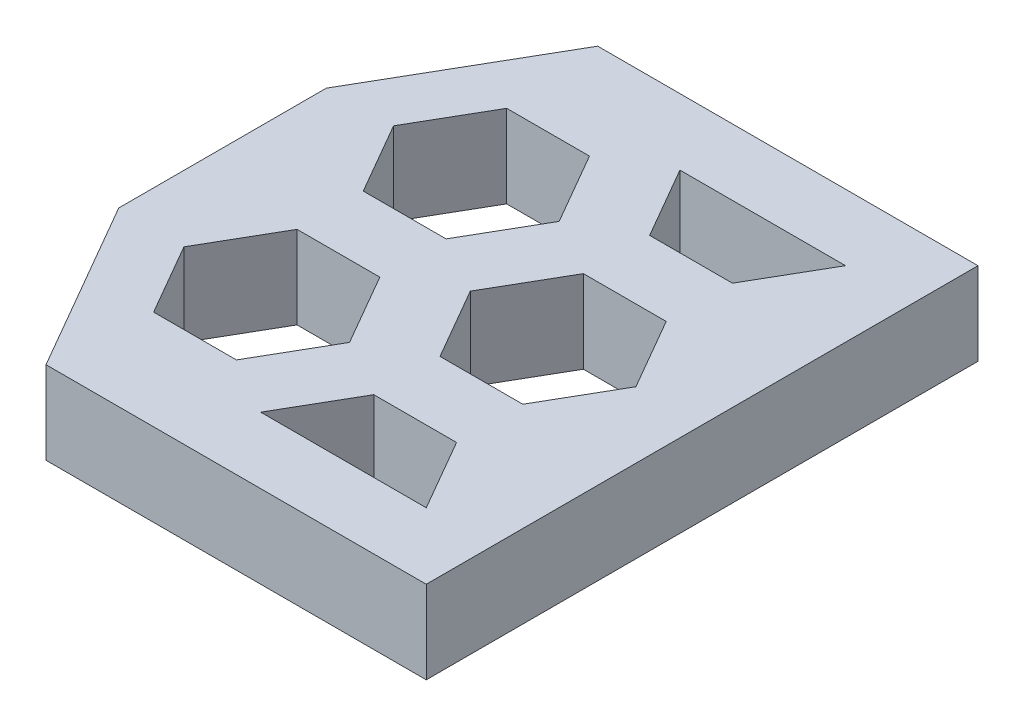
SolidWorks part; units mm, degrees
ref_plane "Front Plane" through (0, 0, 0) normal (0, 0, 1) x (1, 0, 0)
ref_plane "Top Plane" through (0, 0, 0) normal (0, 1, 0) x (1, 0, 0)
ref_plane "Right Plane" through (0, 0, 0) normal (1, 0, 0) x (0, 0, -1)
sketch "Sketch1" plane through (0, 0, 0) normal (0, 1, 0) x (1, 0, 0)
  line L0 (7.4821, 14.6603) -> (12.4821, 14.6603)
  line L1 (0, 0) -> (14.4821, 0)
  line L2 (0, 0) -> (0, 16.6603)
  line L3 (0, 16.6603) -> (14.4821, 16.6603)
  line L4 (14.4821, 0) -> (14.4821, 16.6603)
  line L5 (7, 11.4952) -> (5.75, 13.6603)
  line L6 (5.75, 13.6603) -> (3.25, 13.6603)
  line L7 (3.25, 13.6603) -> (2, 11.4952)
  line L8 (2, 11.4952) -> (3.25, 9.3301)
  line L9 (3.25, 9.3301) -> (5.75, 9.3301)
  line L10 (5.75, 9.3301) -> (7, 11.4952)
  line L11 (7, 5.1651) -> (5.75, 7.3301)
  line L12 (5.75, 7.3301) -> (3.25, 7.3301)
  line L13 (3.25, 7.3301) -> (2, 5.1651)
  line L14 (2, 5.1651) -> (3.25, 3)
  line L15 (3.25, 3) -> (5.75, 3)
  line L16 (5.75, 3) -> (7, 5.1651)
  line L17 (12.4821, 8.3301) -> (11.2321, 10.4952)
  line L18 (11.2321, 10.4952) -> (8.7321, 10.4952)
  line L19 (8.7321, 10.4952) -> (7.4821, 8.3301)
  line L20 (7.4821, 8.3301) -> (8.7321, 6.1651)
  line L21 (8.7321, 6.1651) -> (11.2321, 6.1651)
  line L22 (11.2321, 6.1651) -> (12.4821, 8.3301)
  line L26 (7.4821, 14.6603) -> (8.7321, 12.4952)
  line L27 (8.7321, 12.4952) -> (11.2321, 12.4952)
  line L28 (11.2321, 12.4952) -> (12.4821, 14.6603)
  line L29 (11.2321, 16.8253) -> (9.9821, 16.8253) [skipped]
  line L30 (11.9047, 15.6603) -> (11.8571, 15.7428) [skipped]
  line L31 (7.674, 14.9928) -> (7.6264, 14.9103) [skipped]
  line L32 (7.4821, 2) -> (12.4821, 2)
  line L33 (12.4821, 2) -> (11.2321, 4.1651)
  line L34 (11.2321, 4.1651) -> (8.7321, 4.1651)
  line L35 (8.7321, 4.1651) -> (7.4821, 2)
  line L39 (8.5401, 0.1675) -> (9.1651, -0.9151) [skipped]
  line L40 (9.9821, -0.1651) -> (11.2321, -0.1651) [skipped]
  line L41 (11.424, 0.1675) -> (11.4717, 0.25) [skipped]
  circle A0 centre (4.5, 11.4952) radius 2.1651 construction
  circle A1 centre (4.5, 5.1651) radius 2.1651 construction
  circle A2 centre (9.9821, 8.3301) radius 2.1651 construction
  arc A4 (8.1071, 13.5777) -> (11.8571, 13.5777) centre (9.9821, 14.6603) ccw construction
  arc A5 (11.8571, 3.0825) -> (8.1071, 3.0825) centre (9.9821, 2) ccw construction
  dimension "D1" = 2.5
  dimension "D2" = 2.5
  dimension "D3" = 2
  dimension "D4" = 2.5
  dimension "D5" = 2
  dimension "D6" = 2
  dimension "D7" = 2.5
  dimension "D8" = 2
  dimension "D9" = 2
  dimension "D10" = 2
  dimension "D11" = 2
  dimension "D12" = 2.5
  dimension "D13" = 2
  dimension "D14" = 2
  dimension "D15" = 2
  dimension "D16" = 2
extrude "Boss-Extrude1" add sketch "Sketch1" along normal blind 2.5
chamfer "Chamfer1" distance 3 angle 60 2 edges at (0, 1.25, 0) (0, 1.25, -16.6603)
